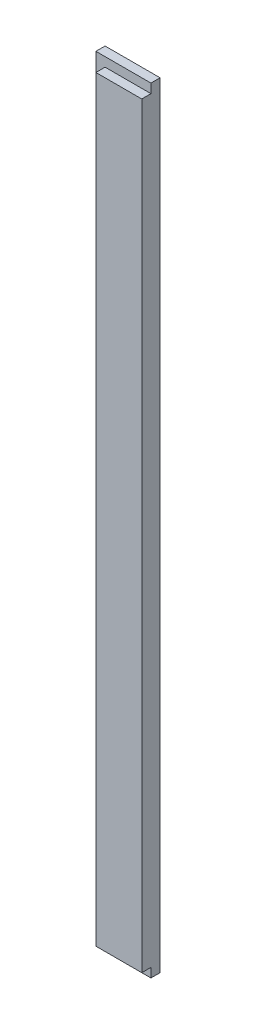
SolidWorks part; units mm, degrees
ref_plane "Front Plane" through (0, 0, 0) normal (0, 0, 1) x (1, 0, 0)
ref_plane "Top Plane" through (0, 0, 0) normal (0, 1, 0) x (1, 0, 0)
ref_plane "Right Plane" through (0, 0, 0) normal (1, 0, 0) x (0, 0, -1)
sketch "Sketch1" plane through (0, 0, 0) normal (0, 0, 1) x (1, 0, 0)
  line L0 (-30, 422.5) -> (30, 422.5)
  line L1 (30, 422.5) -> (30, -422.5)
  line L2 (30, -422.5) -> (-30, -422.5)
  line L3 (-30, -422.5) -> (-30, 422.5)
  point P2 (0, 422.5)
  point P5 (-30, 0)
  dimension "D1" = 60
  dimension "D2" = 845
extrude "Boss-Extrude1" add sketch "Sketch1" along normal blind 20
sketch "Sketch2" plane through (0, 0, 20) normal (0, 0, 1) x (1, 0, 0)
  line L0 (30, 412.5) -> (-20, 412.5)
  line L1 (-20, 412.5) -> (-20, -412.5)
  line L2 (-20, -412.5) -> (30, -412.5)
  line L4 (-30, 422.5) -> (-30, -422.5)
  line L5 (-30, -422.5) -> (30, -422.5)
  line L6 (30, -422.5) -> (30, 422.5)
  line L7 (30, 422.5) -> (-30, 422.5)
  line L8 (-30, 422.5) -> (-30, -422.5)
  line L9 (-30, -422.5) -> (30, -422.5)
  line L10 (30, -422.5) -> (30, -412.5)
  line L11 (30, 422.5) -> (-30, 422.5)
  line L12 (20, -412.5) -> (20, 412.5) construction
  line L13 (20, 412.5) -> (-20, 412.5) construction
  line L14 (-20, -412.5) -> (20, -412.5) construction
  line L15 (30, 412.5) -> (30, 422.5)
  line L16 (30, -422.5) -> (30, 422.5) construction
  dimension "D1" = 0
  dimension "D2" = 10
extrude "Cut-Extrude1" cut sketch "Sketch2" against normal blind 10
